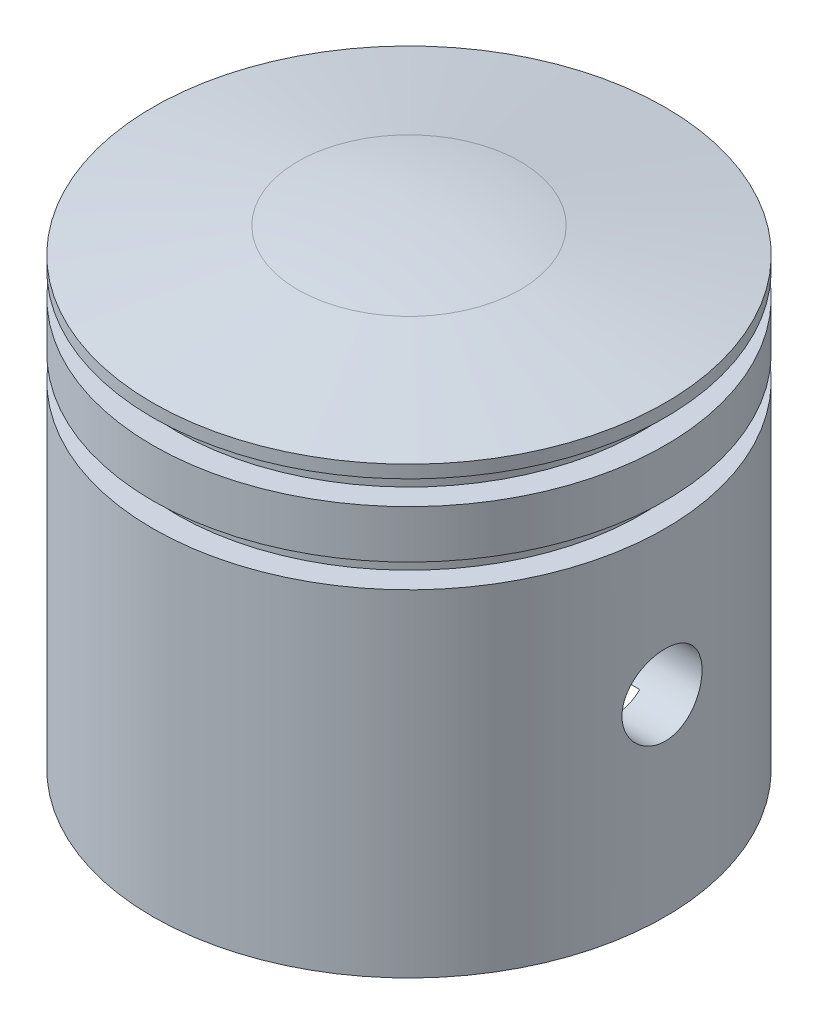
SolidWorks part; units mm, degrees
ref_plane "Front Plane" through (0, 0, 0) normal (0, 0, 1) x (1, 0, 0)
ref_plane "Top Plane" through (0, 0, 0) normal (0, 1, 0) x (1, 0, 0)
ref_plane "Right Plane" through (0, 0, 0) normal (1, 0, 0) x (0, 0, -1)
sketch "Sketch1" plane through (0, 0, 0) normal (0, 0, 1) x (1, 0, 0)
  line L0 (0, 0) -> (16, 0)
  line L1 (16, 0) -> (16, 27.7958)
  line L4 (0, 30) -> (0, 0)
  line L5 (16, 27.7958) -> (6.9459, 29.3923)
  line L7 (0, 30) -> (14.3784, 30) construction
  arc A0 (6.9459, 29.3923) -> (0, 30) centre (0, -10) ccw
  dimension "D3" = 40
  dimension "D1" = 30
  dimension "D2" = 16
  dimension "D4" = 10
revolve "Revolve1" add sketch "Sketch1" angle 360 about L4
sketch "Sketch2" plane through (0, 0, 0) normal (0, 0, 1) x (1, 0, 0)
  line L0 (0, 0) -> (0, 28.8488) construction
  line L1 (-16, 0) -> (16, 0) construction
  line L6 (14.5, 27) -> (18.7834, 27)
  line L7 (14.5, 27) -> (14.5, 25.5)
  line L8 (14.5, 25.5) -> (18.7834, 25.5)
  line L9 (18.7834, 27) -> (18.7834, 25.5)
  line L10 (14.5, 27) -> (18.7834, 25.5) construction
  line L11 (14.5, 25.5) -> (18.7834, 27) construction
  line L12 (14.5, 22.5) -> (19.1017, 22.5)
  line L13 (14.5, 22.5) -> (14.5, 21)
  line L14 (14.5, 21) -> (19.1017, 21)
  line L15 (19.1017, 22.5) -> (19.1017, 21)
  line L16 (14.5, 22.5) -> (19.1017, 21) construction
  line L17 (14.5, 21) -> (19.1017, 22.5) construction
  point P7 (16.6417, 26.25)
  point P12 (16.8009, 21.75)
  dimension "D1" = 3
  dimension "D2" = 1.5
  dimension "D3" = 1.5
  dimension "D4" = 21
  dimension "D5" = 14.5
revolve "Cut-Revolve1" cut sketch "Sketch2" angle 360 about L0
sketch "Sketch3" plane through (0, 0, 0) normal (0, -1, 0) x (1, 0, 0)
  circle A0 centre (0, 0) radius 10
  dimension "D1" = 20
extrude "Cut-Extrude1" cut sketch "Sketch3" against normal blind 24
sketch "Sketch4" plane through (0, 0, 0) normal (0, -1, 0) x (1, 0, 0)
  circle A0 centre (0, 0) radius 13
  dimension "D1" = 26
extrude "Cut-Extrude2" cut sketch "Sketch4" against normal blind 10
sketch "Sketch5" plane through (0, 0, 0) normal (1, 0, 0) x (0, 0, -1)
  circle A0 centre (0, 12) radius 2.5
  dimension "D1" = 5
  dimension "D2" = 12
extrude "Cut-Extrude3" cut sketch "Sketch5" against normal through all both and the other way through all
